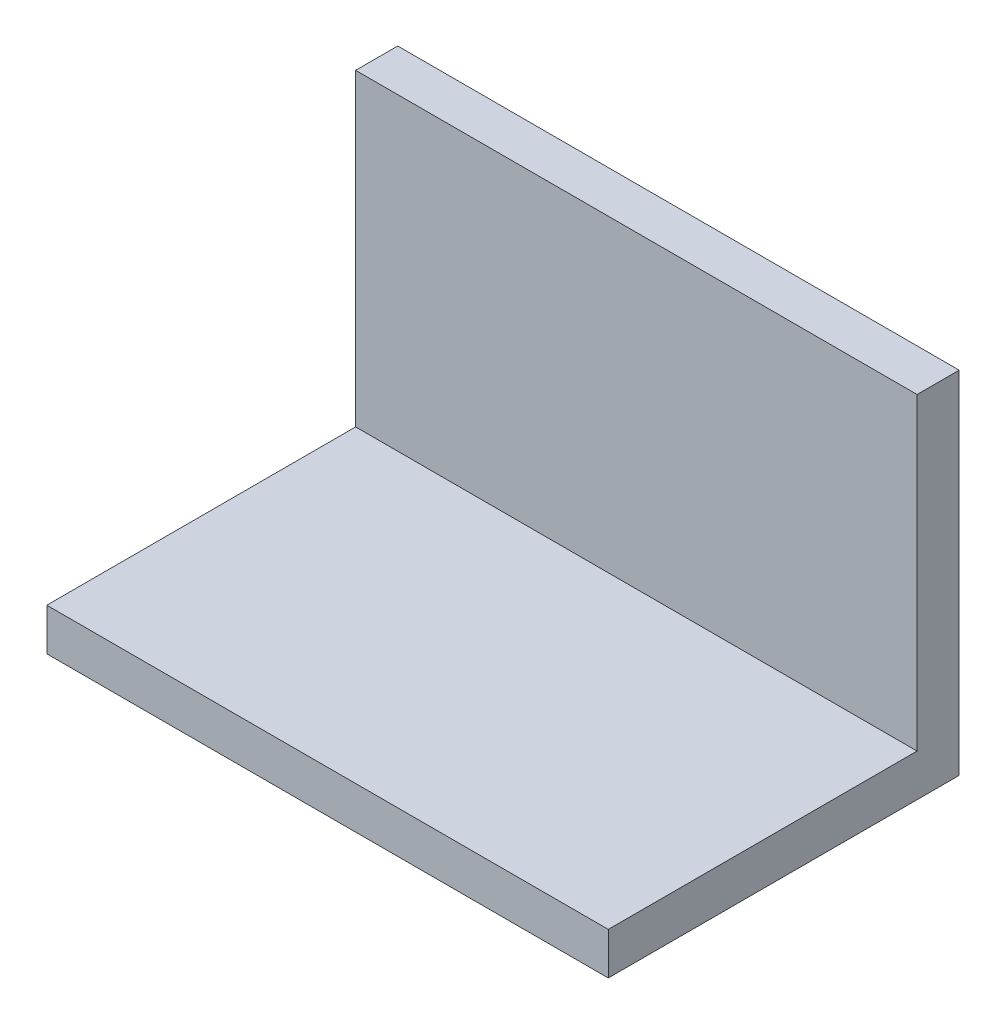
SolidWorks part; units mm, degrees
ref_plane "Alzado" through (0, 0, 0) normal (0, 0, 1) x (1, 0, 0)
ref_plane "Planta" through (0, 0, 0) normal (0, 1, 0) x (1, 0, 0)
ref_plane "Vista lateral" through (0, 0, 0) normal (1, 0, 0) x (0, 0, -1)
sketch "Croquis1" plane through (0, 0, 0) normal (0, 1, 0) x (1, 0, 0)
  line L1 (-40, -25) -> (40, -25)
  line L2 (-40, -25) -> (-40, 25)
  line L3 (-40, 25) -> (40, 25)
  line L4 (40, -25) -> (40, 25)
  line L5 (-40, -25) -> (40, 25) construction
  line L6 (-40, 25) -> (40, -25) construction
  point P0 (0, 0)
  dimension "D1" = 50
  dimension "D2" = 80
extrude "Saliente-Extruir1" add sketch "Croquis1" along normal blind 6
sketch "Croquis2" plane through (0, 6, 0) normal (0, 1, 0) x (1, 0, 0)
  line L0 (-40, 25) -> (-40, -25) construction
  line L1 (-40, 19) -> (40, 19)
  line L2 (-40, 19) -> (-40, 25)
  line L3 (-40, 25) -> (40, 25)
  line L4 (40, 19) -> (40, 25)
  dimension "D1" = 6
extrude "Saliente-Extruir2" add sketch "Croquis2" along normal blind 44
